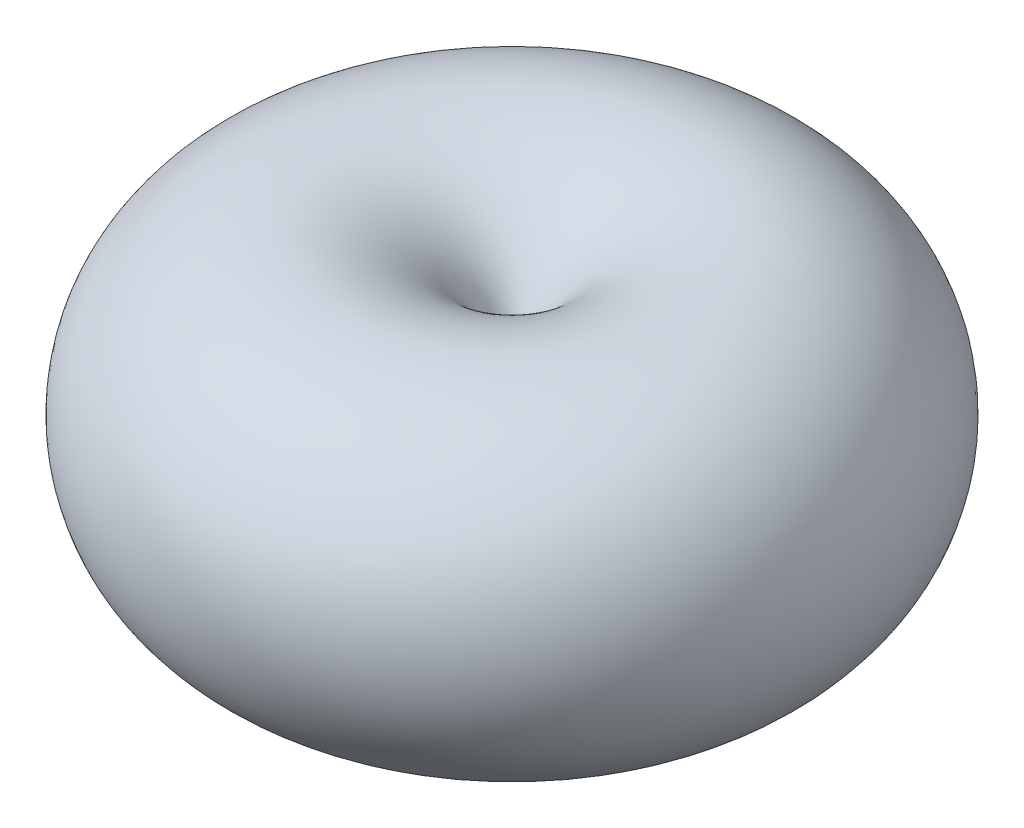
SolidWorks part; units mm, degrees
ref_plane "Front Plane" through (0, 0, 0) normal (0, 0, 1) x (1, 0, 0)
ref_plane "Top Plane" through (0, 0, 0) normal (0, 1, 0) x (1, 0, 0)
ref_plane "Right Plane" through (0, 0, 0) normal (1, 0, 0) x (0, 0, -1)
sketch "Sketch1" plane through (0, 0, 0) normal (0, 0, 1) x (1, 0, 0)
  line L0 (0, 20) -> (0, -20) construction
  circle A0 centre (9.2555, -0.7706) radius 9.2876
revolve "Revolve7" add sketch "Sketch1" angle 360 about L0
